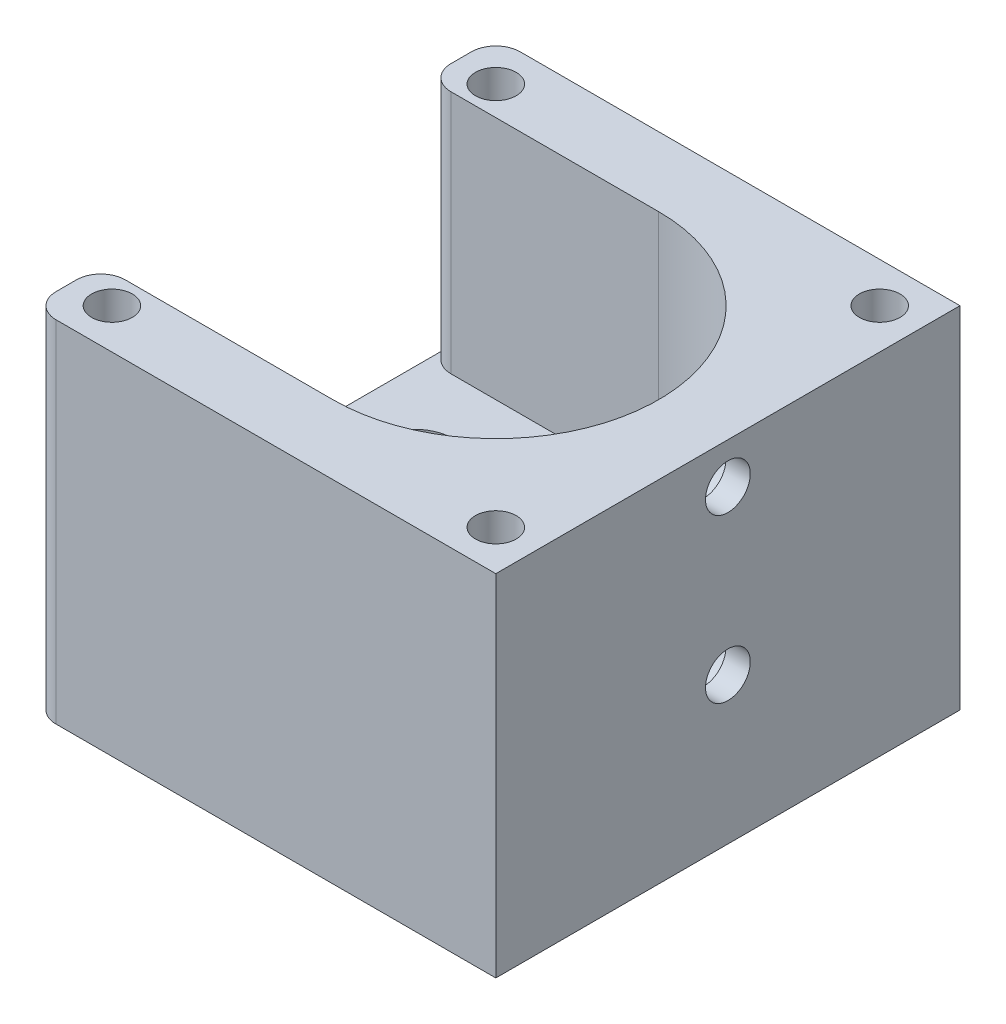
SolidWorks part; units mm, degrees
ref_plane "Front Plane" through (0, 0, 0) normal (0, 0, 1) x (1, 0, 0)
ref_plane "Top Plane" through (0, 0, 0) normal (0, 1, 0) x (1, 0, 0)
ref_plane "Right Plane" through (0, 0, 0) normal (1, 0, 0) x (0, 0, -1)
sketch "Sketch1" plane through (0, 0, 0) normal (0, 1, 0) x (1, 0, 0)
  line L1 (-28.5, 28.5) -> (28.5, 28.5)
  line L2 (-28.5, 28.5) -> (-28.5, -28.5)
  line L3 (-28.5, -28.5) -> (28.5, -28.5)
  line L4 (28.5, 28.5) -> (28.5, -28.5)
  point P4 (0, 28.5)
  point P5 (28.5, 0)
  dimension "D1" = 57
extrude "Boss-Extrude1" add sketch "Sketch1" along normal blind 13
sketch "Sketch2" plane through (0, 13, 0) normal (0, 1, 0) x (1, 0, 0)
  line L0 (0, 20) -> (-28.5, 20)
  line L1 (0, -20) -> (-28.5, -20)
  line L2 (-28.5, -20) -> (-28.5, -28.5)
  line L4 (-28.5, 28.5) -> (-28.5, -28.5)
  line L5 (-28.5, -28.5) -> (28.5, -28.5)
  line L6 (28.5, -28.5) -> (28.5, 28.5)
  line L7 (28.5, 28.5) -> (-28.5, 28.5)
  line L8 (-28.5, 28.5) -> (-28.5, 20)
  line L9 (-28.5, -28.5) -> (28.5, -28.5)
  line L10 (28.5, -28.5) -> (28.5, 28.5)
  line L11 (28.5, 28.5) -> (-28.5, 28.5)
  arc A0 (0, -20) -> (0, 20) centre (0, 0) ccw
  dimension "D2" = 40
  dimension "D1" = 0
extrude "Boss-Extrude2" add sketch "Sketch2" along normal blind 30
sketch "Sketch3" plane through (-28.5, 0, 0) normal (-1, 0, 0) x (0, 0, 1)
  line L0 (20, 43) -> (-20, 43) construction
  line L1 (20, 13) -> (-20, 13) construction
  circle A0 centre (0, 18) radius 2.75
  circle A1 centre (0, 38) radius 2.75
  dimension "D1" = 5.5
  dimension "D2" = 5
  dimension "D3" = 5
extrude "Cut-Extrude1" cut sketch "Sketch3" against normal up to surface (57 mm away) up to face at (28.5, 21.5, 0)
sketch "Sketch4" plane through (-28.5, 0, 0) normal (-1, 0, 0) x (0, 0, 1)
  circle A0 centre (0, 38) radius 4.75
  circle A1 centre (0, 18) radius 4.75
  circle A2 centre (0, 18) radius 2.75 construction
  circle A3 centre (0, 38) radius 2.75 construction
  dimension "D1" = 9.5
extrude "Cut-Extrude6" cut sketch "Sketch4" against normal blind 54
sketch "Sketch5" plane through (0, 43, 0) normal (0, 1, 0) x (1, 0, 0)
  circle A0 centre (-23.57, 23.57) radius 2.5
  circle A1 centre (23.57, 23.57) radius 2.5
  circle A2 centre (23.57, -23.57) radius 2.5
  circle A3 centre (-23.57, -23.57) radius 2.5
  dimension "D1" = 5
  dimension "D2" = 23.57
  dimension "D3" = 23.57
  dimension "D4" = 23.57
  dimension "D5" = 23.57
extrude "Cut-Extrude7" cut sketch "Sketch5" against normal blind 5
sketch "Sketch6" plane through (0, 13, 0) normal (0, 1, 0) x (1, 0, 0)
  line L0 (-28.5, -28.5) -> (28.5, -28.5) construction
  line L1 (-28.5, 20) -> (-28.5, -20) construction
  line L2 (28.5, -28.5) -> (28.5, 28.5) construction
  circle A0 centre (-18.5, 8.5) radius 2.75
  circle A1 centre (8.5, 8.5) radius 2.75
  dimension "D3" = 5.5
  dimension "D1" = 10
  dimension "D2" = 20
  dimension "D4" = 37
extrude "Cut-Extrude8" cut sketch "Sketch6" against normal through all
sketch "Sketch7" plane through (0, 13, 0) normal (0, 1, 0) x (1, 0, 0)
  circle A0 centre (-18.5, 8.5) radius 4.75
  circle A1 centre (8.5, 8.5) radius 4.75
  dimension "D1" = 9.5
extrude "Cut-Extrude9" cut sketch "Sketch7" against normal blind 5
fillet "Fillet1" radius 3 4 edges at (-28.5, 28, 20) (-28.5, 28, -20) (-28.5, 21.5, 28.5) (-28.5, 21.5, -28.5)
